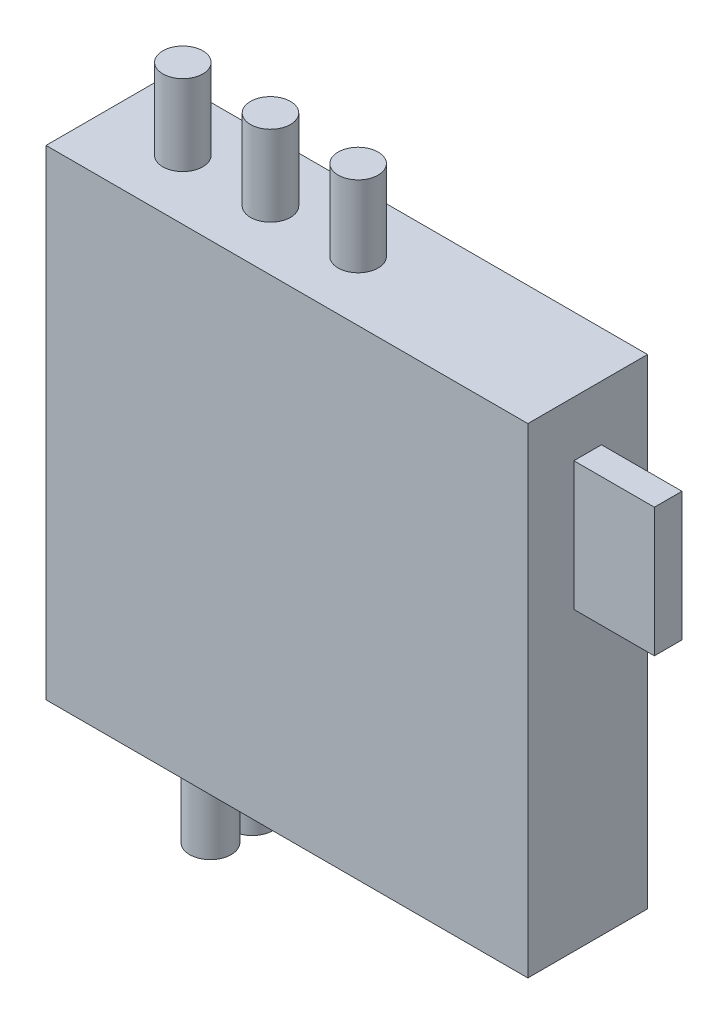
SolidWorks part; units mm, degrees
ref_plane "Front Plane" through (0, 0, 0) normal (0, 0, 1) x (1, 0, 0)
ref_plane "Top Plane" through (0, 0, 0) normal (0, 1, 0) x (1, 0, 0)
ref_plane "Right Plane" through (0, 0, 0) normal (1, 0, 0) x (0, 0, -1)
sketch "Sketch1" plane through (0, 0, 0) normal (0, 1, 0) x (1, 0, 0)
  line L0 (-26.19, -6.505) -> (26.19, 6.505) construction
  line L1 (-26.19, 6.505) -> (26.19, 6.505)
  line L2 (-26.19, 6.505) -> (-26.19, -6.505)
  line L3 (-26.19, -6.505) -> (26.19, -6.505)
  line L4 (26.19, 6.505) -> (26.19, -6.505)
  point P4 (0, 0)
  dimension "D1" = 13.01
  dimension "D2" = 52.38
extrude "Boss-Extrude1" add sketch "Sketch1" along normal blind 52.2
sketch "Sketch2" plane through (0, 0, 0) normal (0, -1, 0) x (-1, 0, 0)
  line L0 (26.19, 6.505) -> (26.19, -6.505) construction
  line L1 (26.19, 0) -> (-26.19, 0) construction
  line L2 (-26.19, -6.505) -> (-26.19, 6.505) construction
  circle A0 centre (12.55, -2.27) radius 2.26
  circle A1 centre (12.55, 2.27) radius 2.26
  dimension "D1" = 4.52
  dimension "D2" = 13.64
  dimension "D3" = 2.27
extrude "Boss-Extrude6" add sketch "Sketch2" along normal blind 8.75
sketch "Sketch3" plane through (0, 52.2, 0) normal (0, 1, 0) x (1, 0, 0)
  line L0 (-26.19, 0) -> (26.19, 0) construction
  line L1 (-26.19, 6.505) -> (-26.19, -6.505) construction
  line L2 (26.19, -6.505) -> (26.19, 6.505) construction
  circle A0 centre (-17.825, 0) radius 2.175
  circle A1 centre (-8.295, 0) radius 2.175
  circle A2 centre (1.235, 0) radius 2.175
  dimension "D1" = 4.35
  dimension "D2" = 8.365
  dimension "D3" = 3
extrude "Boss-Extrude7" add sketch "Sketch3" along normal blind 8.75
sketch "Sketch4" plane through (26.19, 0, 0) normal (1, 0, 0) x (0, 0, -1)
  line L0 (0, 52.2) -> (0, 0) construction
  line L1 (-6.505, 52.2) -> (6.505, 52.2) construction
  line L3 (-1.5, 46.2) -> (1.5, 46.2)
  line L4 (-1.5, 46.2) -> (-1.5, 32.2)
  line L5 (-1.5, 32.2) -> (1.5, 32.2)
  line L6 (1.5, 46.2) -> (1.5, 32.2)
  point P9 (0, 46.2)
  dimension "D1" = 3
  dimension "D2" = 14
  dimension "D3" = 6
extrude "Boss-Extrude8" add sketch "Sketch4" along normal blind 8.75
sketch "Sketch5" plane through (0, 52.2, 0) normal (0, 1, 0) x (1, 0, 0)
  line L0 (-26.19, 0) -> (34.94, 0) construction
  line L1 (34.94, 1.5) -> (34.94, -1.5) construction
  line L3 (-26.19, -6.505) -> (26.19, -6.505) construction
  line L4 (4.375, -6.505) -> (4.375, 6.505) construction
  line L5 (26.19, 6.505) -> (-26.19, 6.505) construction
  point P5 (4.375, 0)
